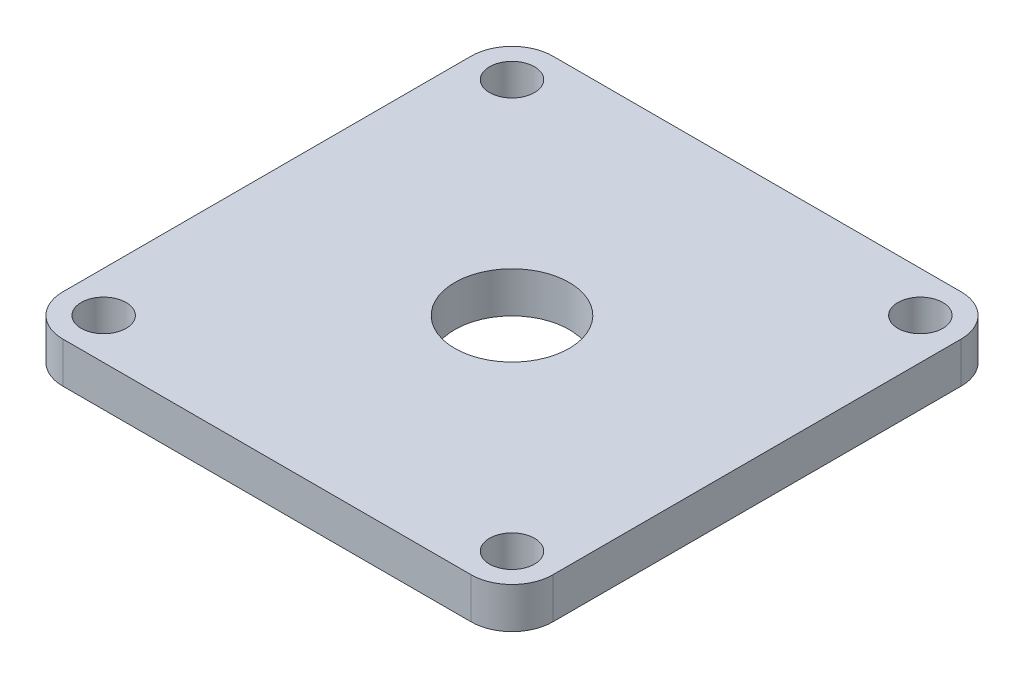
SolidWorks part; units mm, degrees
ref_plane "Front Plane" through (0, 0, 0) normal (0, 0, 1) x (1, 0, 0)
ref_plane "Top Plane" through (0, 0, 0) normal (0, 1, 0) x (1, 0, 0)
ref_plane "Right Plane" through (0, 0, 0) normal (1, 0, 0) x (0, 0, -1)
sketch "Sketch1" plane through (0, 0, 0) normal (0, 1, 0) x (1, 0, 0)
  line L1 (30, 30) -> (-30, 30)
  line L2 (30, 30) -> (30, -30)
  line L3 (30, -30) -> (-30, -30)
  line L4 (-30, 30) -> (-30, -30)
  line L5 (30, 30) -> (-30, -30) construction
  line L6 (30, -30) -> (-30, 30) construction
  point P0 (0, 0)
  dimension "D1" = 60
  dimension "D2" = 60
extrude "Boss-Extrude1" add sketch "Sketch1" along normal blind 5
sketch "Sketch2" plane through (0, 5, 0) normal (0, 1, 0) x (1, 0, 0)
  line L0 (30, -30) -> (30, 30) construction
  line L1 (30, 30) -> (-30, 30) construction
  circle A0 centre (25, 25) radius 2.75
  circle A1 centre (-25, 25) radius 2.75
  circle A2 centre (-25, -25) radius 2.75
  circle A3 centre (25, -25) radius 2.75
  dimension "D1" = 5.5
  dimension "D2" = 5
  dimension "D3" = 5
  dimension "D4" = 2
  dimension "D5" = 2
extrude "Cut-Extrude1" cut sketch "Sketch2" against normal blind 5
fillet "Fillet2" radius 5 4 edges at (-30, 2.5, -30) (-30, 2.5, 30) (30, 2.5, 30) (30, 2.5, -30)
sketch "Sketch3" plane through (0, 5, 0) normal (0, 1, 0) x (1, 0, 0)
  circle A0 centre (0, 0) radius 7
  dimension "D1" = 14
extrude "Cut-Extrude2" cut sketch "Sketch3" against normal blind 5
